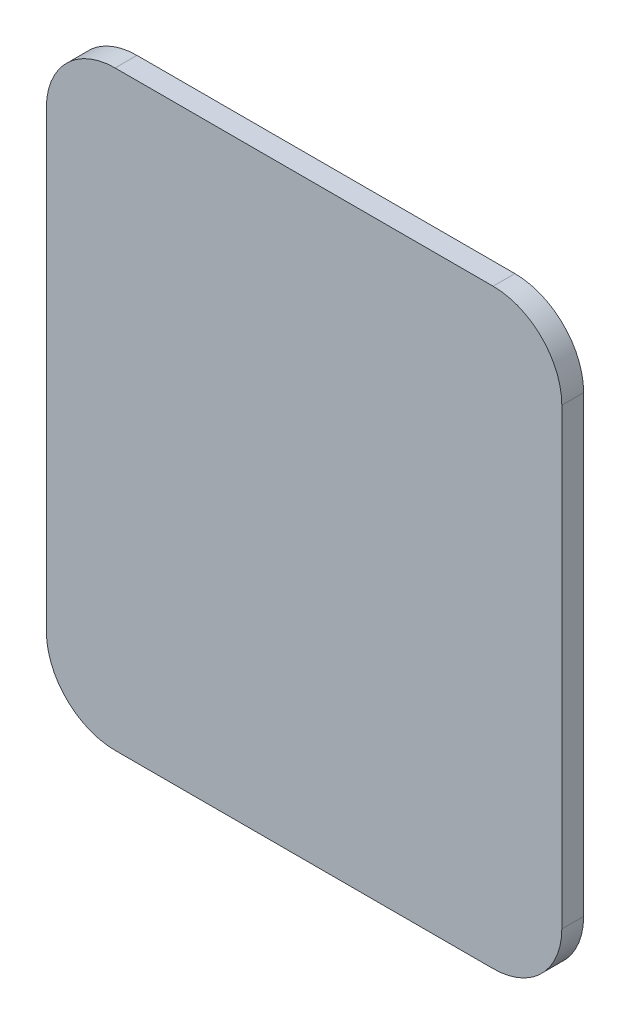
SolidWorks part; units mm, degrees
ref_plane "Front Plane" through (0, 0, 0) normal (0, 0, 1) x (1, 0, 0)
ref_plane "Top Plane" through (0, 0, 0) normal (0, 1, 0) x (1, 0, 0)
ref_plane "Right Plane" through (0, 0, 0) normal (1, 0, 0) x (0, 0, -1)
sketch "Sketch1" plane through (0, 0, 0) normal (0, 0, 1) x (1, 0, 0)
  line L0 (-55, 0) -> (55, 0)
  line L1 (-75, 20) -> (-75, 152)
  line L2 (75, 20) -> (75, 152)
  line L3 (-55, 172) -> (55, 172)
  arc A0 (75, 152) -> (55, 172) centre (55, 152) ccw
  arc A1 (-55, 172) -> (-75, 152) centre (-55, 152) ccw
  arc A2 (-75, 20) -> (-55, 0) centre (-55, 20) ccw
  arc A3 (55, 0) -> (75, 20) centre (55, 20) ccw
  point P3 (0, 0)
  point P10 (-75, 172)
  point P13 (-75, 0)
  point P16 (75, 0)
  dimension "D3" = 20
  dimension "D1" = 150
  dimension "D2" = 172
extrude "Boss-Extrude1" add sketch "Sketch1" along normal blind 6.35
sketch "Sketch3" plane through (0, 0, 6.35) normal (0, 0, 1) x (1, 0, 0)
  circle A0 centre (55.062, 199.9516) radius 3.9666
  circle A1 centre (-58.2167, 198.8503) radius 3.9666
  circle A2 centre (53.7656, 333.2242) radius 3.9666
  circle A3 centre (-59.513, 332.1229) radius 3.9666
extrude "Cut-Extrude1" [suppressed] cut sketch "Sketch3" against normal through all
sketch "Sketch4" plane through (0, 0, 0) normal (0, 0, -1) x (-1, 0, 0)
  line L0 (1.0498, -47.5058) -> (1.0498, 20.9872) construction
  line L1 (75, 152) -> (75, 20) construction
  line L2 (75, 152) -> (75, 20)
